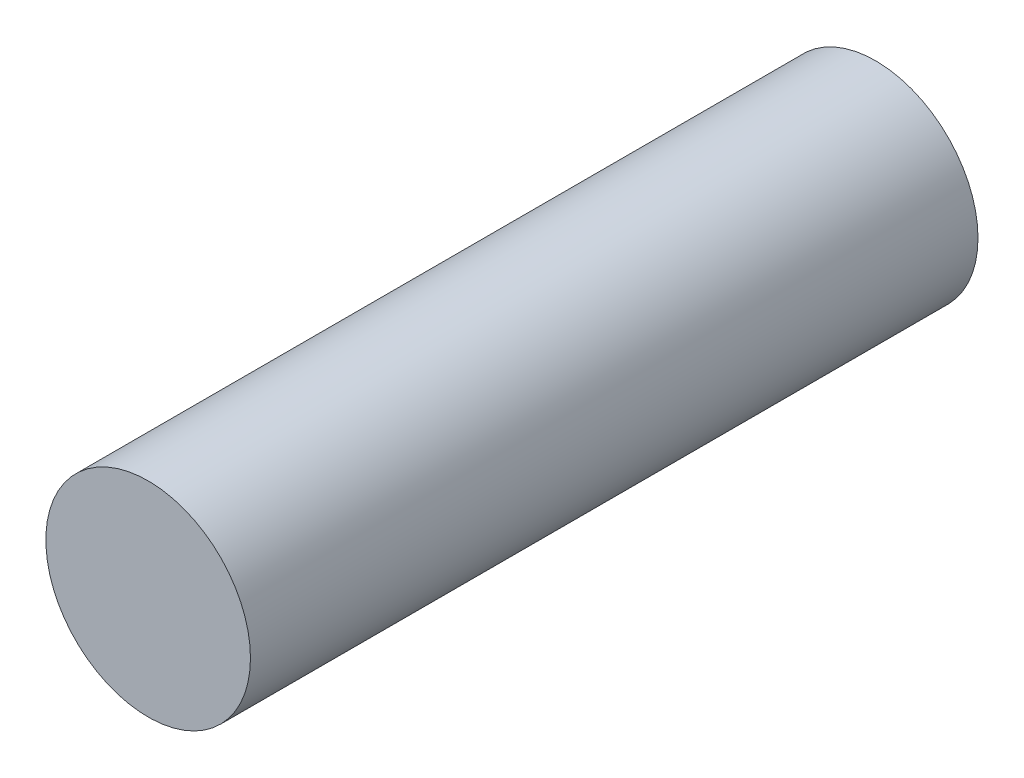
SolidWorks part; units mm, degrees
ref_plane "Front Plane" through (0, 0, 0) normal (0, 0, 1) x (1, 0, 0)
ref_plane "Top Plane" through (0, 0, 0) normal (0, 1, 0) x (1, 0, 0)
ref_plane "Right Plane" through (0, 0, 0) normal (1, 0, 0) x (0, 0, -1)
sketch "Sketch1" plane through (0, 0, 0) normal (0, 0, 1) x (1, 0, 0)
  circle A0 centre (0, 0) radius 2.25
  dimension "D1" = 4.5
extrude "Boss-Extrude1" add sketch "Sketch1" along normal blind 16
